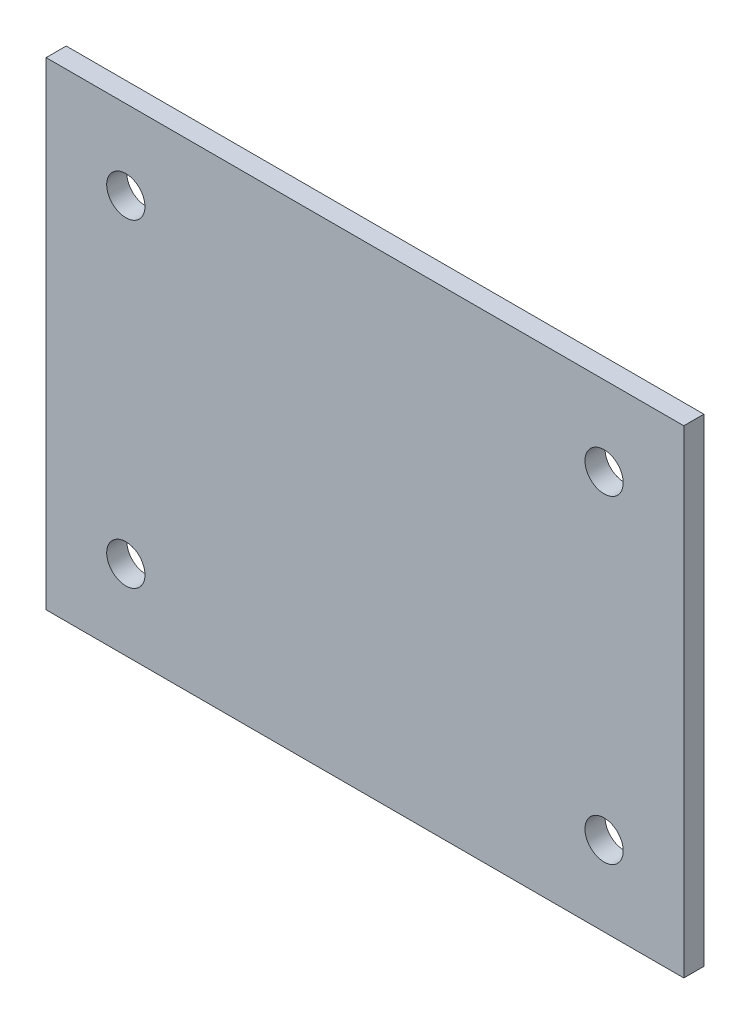
SolidWorks part; units mm, degrees
ref_plane "Front" through (0, 0, 0) normal (0, 0, 1) x (1, 0, 0)
ref_plane "Top" through (0, 0, 0) normal (0, 1, 0) x (1, 0, 0)
ref_plane "Right" through (0, 0, 0) normal (1, 0, 0) x (0, 0, -1)
sketch "Sketch1" plane through (0, 0, 0) normal (0, 0, 1) x (1, 0, 0)
  line L1 (0, 0) -> (50.8, 0)
  line L2 (0, 0) -> (0, -38.1)
  line L3 (0, -38.1) -> (50.8, -38.1)
  line L4 (50.8, 0) -> (50.8, -38.1)
  dimension "D1" = 38.1
  dimension "D2" = 50.8
extrude "Extrude1" add sketch "Sketch1" along normal blind 1.6002
sketch "Sketch2" plane through (0, 0, 1.6002) normal (0, 0, 1) x (1, 0, 0)
  line L0 (50.8, 0) -> (0, 0) construction
  line L1 (0, 0) -> (0, -38.1) construction
  circle A1 centre (6.35, -6.35) radius 1.524
  dimension "D1" = 3.048
  dimension "D2" = 6.35
  dimension "D3" = 6.35
extrude "Cut-Extrude1" cut sketch "Sketch2" against normal blind 1.6002
pattern_linear "LPattern1" count 2 spacing 38.1 along (1, 0, 0) count 2 spacing 25.4 along (0, -1, 0) of "Cut-Extrude1"
